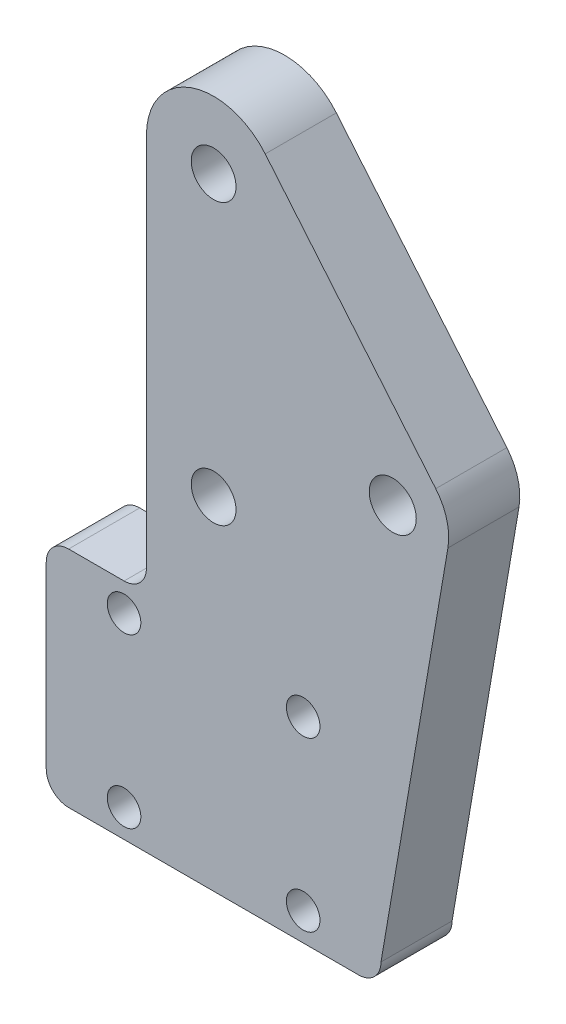
SolidWorks part; units mm, degrees
ref_plane "Front Plane" through (0, 0, 0) normal (0, 0, 1) x (1, 0, 0)
ref_plane "Top Plane" through (0, 0, 0) normal (0, 1, 0) x (1, 0, 0)
ref_plane "Right Plane" through (0, 0, 0) normal (1, 0, 0) x (0, 0, -1)
sketch "Sketch1" plane through (0, 0, 0) normal (0, 0, 1) x (1, 0, 0)
  line L0 (25.95, 316.2243) -> (25.95, 10.5) construction
  line L1 (13.95, 316.2243) -> (13.95, 10.5) construction
  line L2 (5, 10) -> (34.9, 10) construction
  line L3 (34.9, -9.5) -> (34.9, -4.9) construction
  line L4 (34.9, -10) -> (5, -10) construction
  line L5 (5, -9.5) -> (5, -4.9) construction
  line L6 (25.95, 45.5) -> (25.95, 10)
  line L7 (13.95, 45.5) -> (13.95, 10)
  line L8 (5, 10) -> (13.95, 10)
  line L9 (34.9, -10) -> (34.9, 10)
  line L10 (34.9, -10) -> (5, -10)
  line L11 (5, -10) -> (5, 10)
  line L12 (25.95, 10) -> (34.9, 10)
  circle A0 centre (19.95, 20.5) radius 1.75 construction
  circle A1 centre (27.95, -7.5) radius 1.5 construction
  circle A2 centre (11.95, -7.5) radius 1.5 construction
  circle A3 centre (27.95, 7.5) radius 1.5 construction
  circle A4 centre (11.95, 7.5) radius 1.5 construction
  circle A5 centre (19.95, 20.5) radius 1.75 construction
  circle A6 centre (27.95, -7.5) radius 1.5
  circle A7 centre (11.95, -7.5) radius 1.5
  circle A8 centre (27.95, 7.5) radius 1.5
  circle A9 centre (11.95, 7.5) radius 1.5
  circle A10 centre (19.95, 45.5) radius 1.75 construction
  circle A11 centre (19.95, 45.5) radius 1.75 construction
  arc A12 (25.95, 45.5) -> (13.95, 45.5) centre (19.95, 45.5) ccw
  circle A13 centre (19.95, 45.5) radius 2
  circle A14 centre (19.95, 20.5) radius 2
  dimension "D1" = 4
extrude "Boss-Extrude1" add sketch "Sketch1" along normal blind 6.35
fillet "Fillet1" radius 2 6 edges at (25.95, 10, 3.175) (34.9, 10, 3.175) (34.9, -10, 3.175) (5, -10, 3.175) (5, 10, 3.175) (13.95, 10, 3.175)
sketch "Sketch2" plane through (0, 0, 6.35) normal (0, 0, 1) x (1, 0, 0)
  line L0 (19.95, 45.5) -> (19.95, -10) construction
  line L1 (34.9, -10) -> (5, -10) construction
  line L2 (24.5595, 49.3408) -> (39.7913, 31.0607)
  line L3 (34.9, -8) -> (40.8787, 27.0185)
  line L4 (25.95, 12) -> (25.95, 45.5) construction
  line L5 (32.9, 10) -> (27.95, 10) construction
  line L6 (34.9, -8) -> (34.9, 8) construction
  line L7 (34.9, -8) -> (34.9, 8)
  line L8 (32.9, 10) -> (27.95, 10)
  line L9 (25.95, 12) -> (25.95, 45.5)
  arc A0 (40.8787, 27.0185) -> (39.7913, 31.0607) centre (35.95, 27.86) ccw
  circle A1 centre (35.95, 27.86) radius 2.1
  arc A2 (25.95, 45.5) -> (13.95, 45.5) centre (19.95, 45.5) ccw construction
  arc A3 (25.95, 12) -> (27.95, 10) centre (27.95, 12) ccw construction
  arc A4 (25.95, 45.5) -> (13.95, 45.5) centre (19.95, 45.5) ccw construction
  arc A5 (34.9, 8) -> (32.9, 10) centre (32.9, 8) ccw construction
  arc A6 (34.9, 8) -> (32.9, 10) centre (32.9, 8) ccw
  arc A7 (25.95, 45.5) -> (24.5595, 49.3408) centre (19.95, 45.5) ccw
  arc A8 (25.95, 12) -> (27.95, 10) centre (27.95, 12) ccw
  point P8 (35.95, 22.86)
  point P18 (0, 0)
  point P19 (39.7241, 31.1397)
  point P20 (0, 0)
  dimension "D1" = 10
  dimension "D4" = 4.2
  dimension "D2" = 16
  dimension "D3" = 32.86
extrude "Boss-Extrude2" add sketch "Sketch2" against normal up to surface (6.35 mm away) up to face at (19.95, 10.0123, 0)
